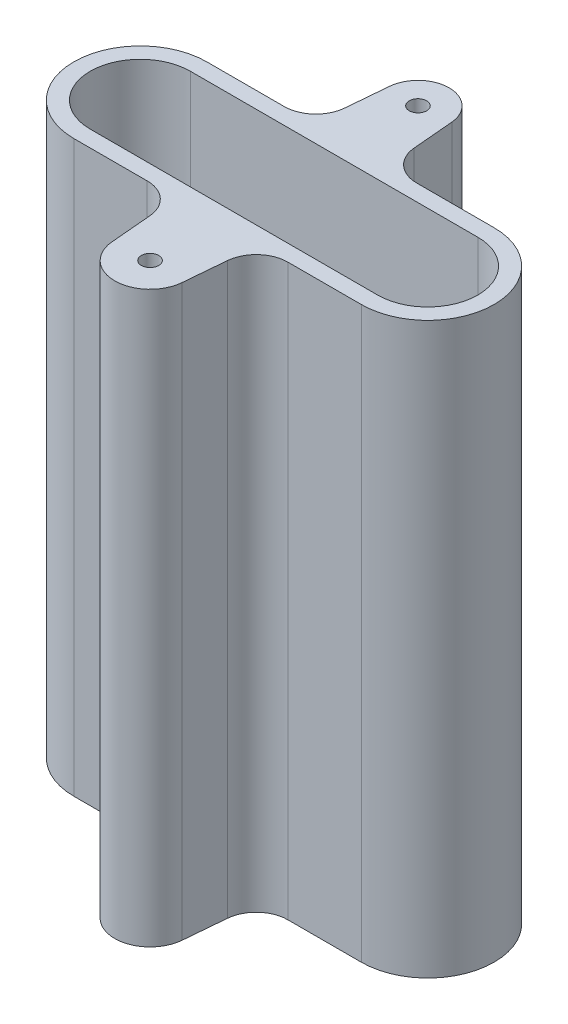
SolidWorks part; units mm, degrees
material "Gray Cast Iron"
ref_plane "Front Plane" through (0, 0, 0) normal (0, 0, 1) x (1, 0, 0)
ref_plane "Top Plane" through (0, 0, 0) normal (0, 1, 0) x (1, 0, 0)
ref_plane "Right Plane" through (0, 0, 0) normal (1, 0, 0) x (0, 0, -1)
sketch "Sketch1" plane through (0, 0, 0) normal (0, 1, 0) x (1, 0, 0)
  line L0 (-13.625, 0) -> (13.625, 0) construction
  line L1 (-20.2125, 0) -> (20.2125, 0) construction
  line L2 (-13.625, 4.75) -> (13.625, 4.75)
  line L3 (-13.625, -4.75) -> (13.625, -4.75)
  line L4 (0, -5.225) -> (0, 5.225) construction
  line L5 (-2.9454, 12.9577) -> (-3.2883, 9.0385)
  line L6 (2.9454, 12.9577) -> (3.2883, 9.0385)
  line L7 (-3.3323, -12.9915) -> (-3.6782, -9.0385)
  line L8 (3.3323, -12.9915) -> (3.6782, -9.0385)
  line L9 (-13.625, 6.3) -> (-6.2769, 6.3)
  line L10 (6.2769, 6.3) -> (13.625, 6.3)
  line L11 (13.625, -6.3) -> (6.6668, -6.3)
  line L12 (-6.6668, -6.3) -> (-13.625, -6.3)
  arc A0 (-13.625, 4.75) -> (-13.625, -4.75) centre (-13.625, 0) ccw
  arc A1 (13.625, -4.75) -> (13.625, 4.75) centre (13.625, 0) ccw
  circle A2 centre (0, 12.7) radius 0.825
  circle A3 centre (0, -12.7) radius 0.825
  arc A4 (2.9454, 12.9577) -> (-2.9454, 12.9577) centre (0, 12.7) ccw
  arc A5 (-3.3323, -12.9915) -> (3.3323, -12.9915) centre (0, -12.7) ccw
  arc A6 (13.625, 6.3) -> (13.625, -6.3) centre (13.625, 0) cw
  arc A7 (-13.625, 6.3) -> (-13.625, -6.3) centre (-13.625, 0) ccw
  arc A8 (-6.2769, 6.3) -> (-3.2883, 9.0385) centre (-6.2769, 9.3) ccw
  arc A9 (6.2769, 6.3) -> (3.2883, 9.0385) centre (6.2769, 9.3) cw
  arc A10 (3.6782, -9.0385) -> (6.6668, -6.3) centre (6.6668, -9.3) cw
  arc A11 (-3.6782, -9.0385) -> (-6.6668, -6.3) centre (-6.6668, -9.3) ccw
  point P5 (0, 0)
  point P38 (-3.9178, -6.3)
  dimension "D4" = 1.65
  dimension "D11" = 3
  dimension "D1" = 9.5
  dimension "D2" = 27.25
  dimension "D3" = 13.625
  dimension "D5" = 25.4
  dimension "D6" = 12.7
  dimension "D7" = 5
  dimension "D8" = 5
  dimension "D9" = 5
  dimension "D10" = 5
  dimension "D12" = 1.55
extrude "Extrude1" add sketch "Sketch1" along normal blind 54
